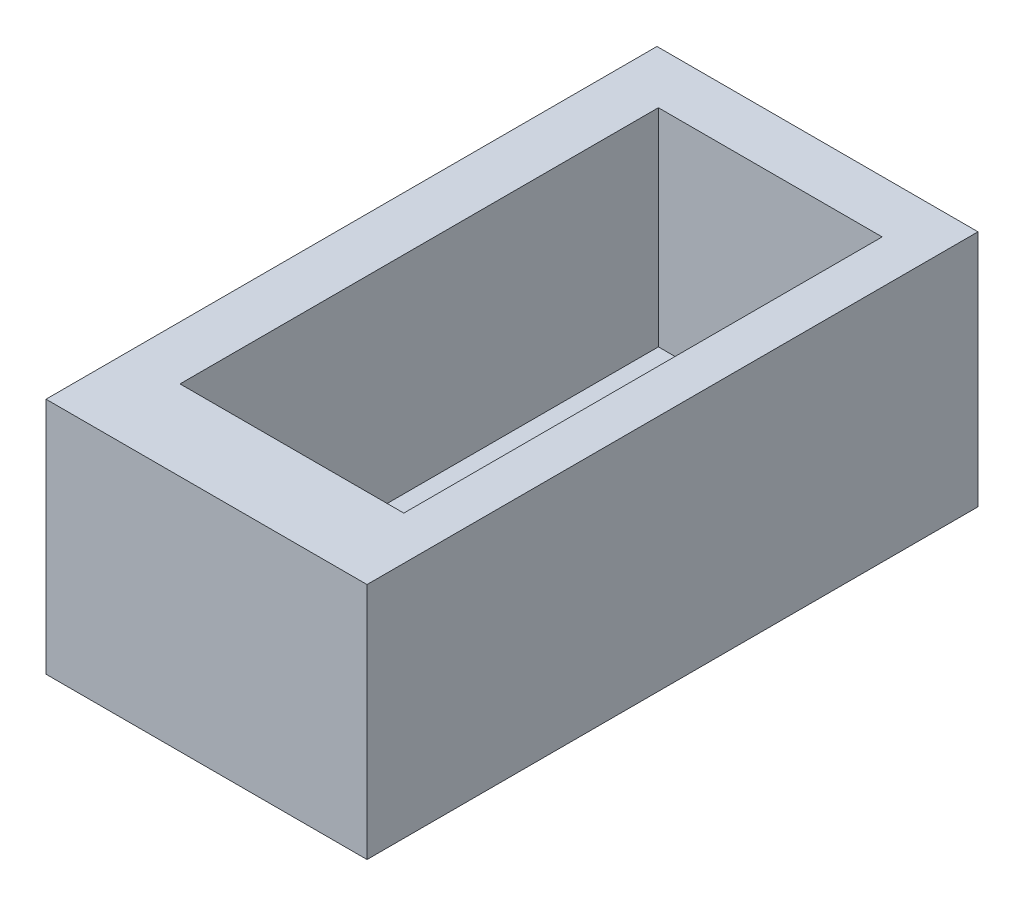
SolidWorks part; units mm, degrees
material "6061-T6 (SS)"
ref_plane "Front Plane" through (0, 0, 0) normal (0, 0, 1) x (1, 0, 0)
ref_plane "Top Plane" through (0, 0, 0) normal (0, 1, 0) x (1, 0, 0)
ref_plane "Right Plane" through (0, 0, 0) normal (1, 0, 0) x (0, 0, -1)
sketch "Sketch1" plane through (0, 0, 0) normal (0, 1, 0) x (1, 0, 0)
  line L1 (15.5, -29.5) -> (-15.5, -29.5)
  line L2 (15.5, -29.5) -> (15.5, 29.5)
  line L3 (15.5, 29.5) -> (-15.5, 29.5)
  line L4 (-15.5, -29.5) -> (-15.5, 29.5)
  line L5 (15.5, -29.5) -> (-15.5, 29.5) construction
  line L6 (15.5, 29.5) -> (-15.5, -29.5) construction
  point P0 (0, 0)
  dimension "D1" = 31
  dimension "D2" = 59
extrude "Boss-Extrude1" add sketch "Sketch1" along normal blind 23
sketch "Sketch2" plane through (0, 23, 0) normal (0, 1, 0) x (1, 0, 0)
  line L1 (-10.3075, 24.4444) -> (11.3017, 24.4444)
  line L2 (-10.3075, 24.4444) -> (-10.3075, -21.7499)
  line L3 (-10.3075, -21.7499) -> (11.3017, -21.7499)
  line L4 (11.3017, 24.4444) -> (11.3017, -21.7499)
  point P4 (11.3017, 24.4444)
extrude "Cut-Extrude1" cut sketch "Sketch2" against normal blind 20
